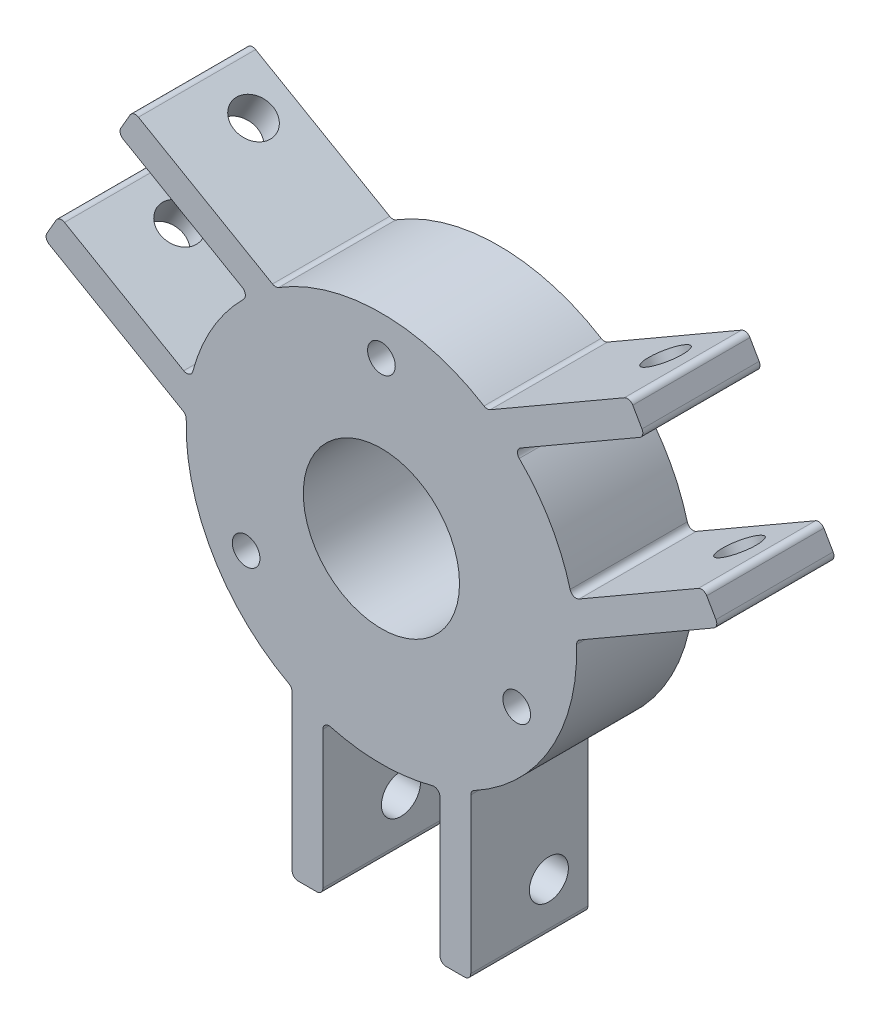
SolidWorks part; units mm, degrees
material "6061-T6 (SS)"
ref_plane "Plan de face" through (0, 0, 0) normal (0, 0, 1) x (1, 0, 0)
ref_plane "Plan de dessus" through (0, 0, 0) normal (0, 1, 0) x (1, 0, 0)
ref_plane "Plan de droite" through (0, 0, 0) normal (1, 0, 0) x (0, 0, -1)
sketch "Esquisse1" plane through (0, 0, 0) normal (0, 0, 1) x (1, 0, 0)
  line L0 (0, 0) -> (0, 50000) construction
  line L1 (0, 0) -> (-27.4963, -15.875) construction
  line L2 (0, 0) -> (27.4963, -15.875) construction
  circle A0 centre (0, 0) radius 31.75
  circle A1 centre (0, 0) radius 12.7
  circle A2 centre (0, 0) radius 25.4
  circle A3 centre (0, 25.4) radius 2.25
  circle A4 centre (-21.997, -12.7) radius 2.25
  circle A5 centre (21.997, -12.7) radius 2.25
  dimension "D1" = 25.4
  dimension "D2" = 63.5
  dimension "D5" = 50.8
  dimension "D6" = 4.5
  dimension "D3" = 120
  dimension "D4" = 120
extrude "Boss.-Extru.1" add sketch "Esquisse1" along normal blind 19.05 contours A0 A5 A2 A4 A3 | A5 A2 A3 A4 A1
sketch "Esquisse2" plane through (0, 0, 19.05) normal (0, 0, 1) x (1, 0, 0)
  line L0 (0, 0) -> (0, 50000) construction
  line L1 (0, 0) -> (-43301.2702, 25000) construction
  line L2 (0, 0) -> (43301.2702, 25000) construction
  line L3 (46.2964, 29.8124) -> (-24953.7036, 43331.0825) construction
  line L4 (42.8689, 35.7489) -> (21.4673, 23.3927)
  line L5 (42.8689, 35.7489) -> (40.3689, 40.079)
  line L6 (40.3689, 40.079) -> (17.1878, 26.6954)
  line L7 (21.4673, 23.3927) -> (17.1878, 26.6954)
  line L8 (30.9923, 6.8949) -> (31.7128, 1.5373)
  line L9 (54.8939, 14.921) -> (31.7128, 1.5373)
  line L10 (52.3939, 19.2511) -> (54.8939, 14.921)
  line L11 (52.3939, 19.2511) -> (30.9923, 6.8949)
  line L12 (14.525, -55) -> (14.525, -28.2327)
  line L13 (9.525, -55) -> (9.525, -30.2876)
  line L14 (9.525, -55) -> (14.525, -55)
  line L15 (9.525, -30.2876) -> (14.525, -28.2327)
  line L16 (-9.525, -30.2876) -> (-14.525, -28.2327)
  line L17 (-9.525, -55) -> (-9.525, -30.2876)
  line L18 (-14.525, -55) -> (-14.525, -28.2327)
  line L19 (-9.525, -55) -> (-14.525, -55)
  line L20 (-54.8939, 14.921) -> (-31.7128, 1.5373)
  line L21 (-52.3939, 19.2511) -> (-30.9923, 6.8949)
  line L22 (-52.3939, 19.2511) -> (-54.8939, 14.921)
  line L23 (-30.9923, 6.8949) -> (-31.7128, 1.5373)
  line L24 (-21.4673, 23.3927) -> (-17.1878, 26.6954)
  line L25 (-42.8689, 35.7489) -> (-21.4673, 23.3927)
  line L26 (-40.3689, 40.079) -> (-17.1878, 26.6954)
  line L27 (-42.8689, 35.7489) -> (-40.3689, 40.079)
  circle A0 centre (0, 0) radius 31.75 construction
  point P38 (0, 0)
  dimension "D1" = 60
  dimension "D2" = 60
  dimension "D3" = 9.525
  dimension "D4" = 5
  dimension "D5" = 55
  dimension "D6" = 3
extrude "Boss.-Extru.2" add sketch "Esquisse2" against normal up to surface (19.05 mm away) up to face at (24.247, -12.7, 0)
sketch "Esquisse3" plane through (7.2625, 12.579, 0) normal (0.5, 0.866, 0) x (0.866, -0.5, 0)
  line L1 (-55, 0) -> (-55, -19.05) construction
  line L3 (-28.2327, -19.05) -> (-55, -19.05) construction
  circle A0 centre (-47.0625, -6.35) radius 3.175
  dimension "D1" = 6.35
  dimension "D2" = 7.9375
  dimension "D3" = 12.7
extrude "Enlèv. mat.-Extru.1" cut sketch "Esquisse3" against normal through all
sketch "Esquisse4" plane through (-7.2625, 12.579, 0) normal (-0.5, 0.866, 0) x (0.866, 0.5, 0)
  line L0 (55, -19.05) -> (28.2327, -19.05) construction
  line L1 (55, 0) -> (55, -19.05) construction
  circle A0 centre (47.0625, -6.35) radius 3.175
  dimension "D1" = 6.35
  dimension "D2" = 7.9375
  dimension "D3" = 12.7
extrude "Enlèv. mat.-Extru.2" cut sketch "Esquisse4" against normal through all
sketch "Esquisse5" plane through (14.525, 0, 0) normal (1, 0, 0) x (0, 0, -1)
  line L0 (-19.05, -55) -> (-19.05, -28.2327) construction
  line L1 (0, -55) -> (-19.05, -55) construction
  circle A0 centre (-6.35, -47.0625) radius 3.175
  dimension "D2" = 6.35
  dimension "D1" = 7.9375
  dimension "D3" = 12.7
extrude "Enlèv. mat.-Extru.3" cut sketch "Esquisse5" against normal through all
fillet "Congé1" radius 1 24 edges at (-17.1878, 26.6954, 9.525) (17.1878, 26.6954, 9.525) (21.4673, 23.3927, 9.525) (30.9923, 6.8949, 9.525) (40.3689, 40.079, 9.525) (42.8689, 35.7489, 9.525) (52.3939, 19.2511, 9.525) (54.8939, 14.921, 9.525) (31.7128, 1.5373, 9.525) (14.525, -28.2327, 9.525) (9.525, -30.2876, 9.525) (-9.525, -30.2876, 9.525) (14.525, -55, 9.525) (9.525, -55, 9.525) (-9.525, -55, 9.525) (-14.525, -55, 9.525) (-14.525, -28.2327, 9.525) (-31.7128, 1.5373, 9.525) (-21.4673, 23.3927, 9.525) (-30.9923, 6.8949, 9.525) (-54.8939, 14.921, 9.525) (-52.3939, 19.2511, 9.525) (-42.8689, 35.7489, 9.525) (-40.3689, 40.079, 9.525)
